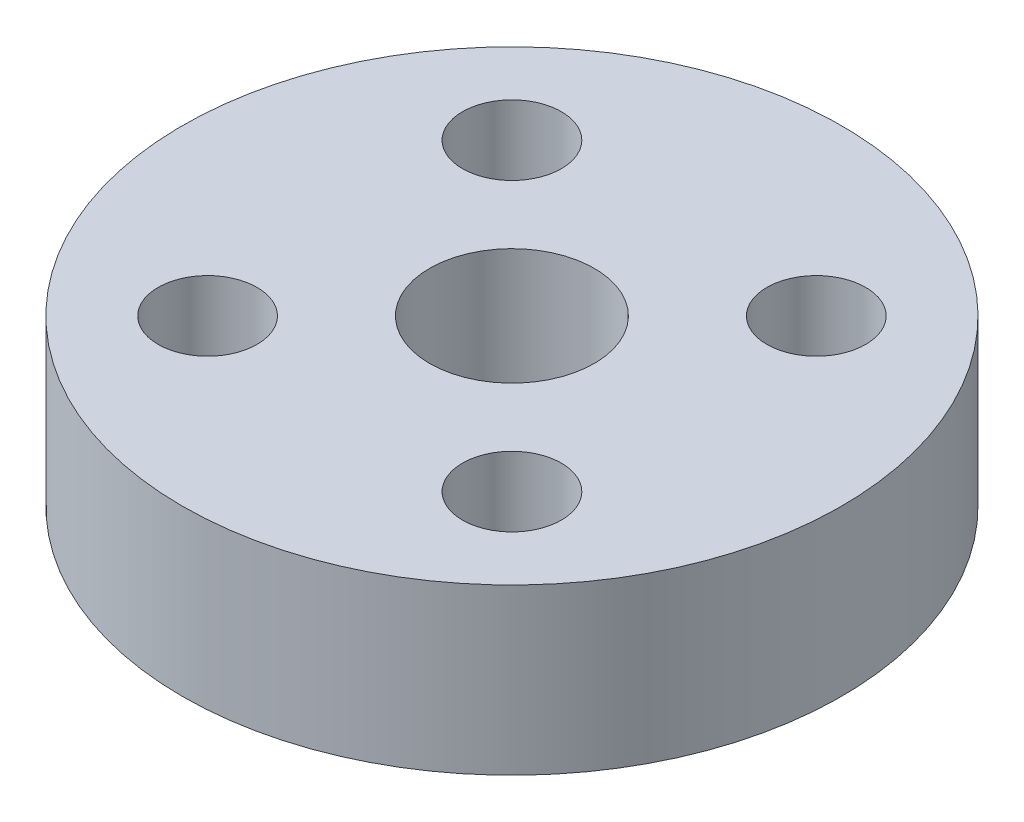
SolidWorks part; units mm, degrees
ref_plane "Спереди" through (0, 0, 0) normal (0, 0, 1) x (1, 0, 0)
ref_plane "Сверху" through (0, 0, 0) normal (0, 1, 0) x (1, 0, 0)
ref_plane "Справа" through (0, 0, 0) normal (1, 0, 0) x (0, 0, -1)
sketch "Эскиз1" plane through (0, 0, 0) normal (0, 1, 0) x (1, 0, 0)
  line L0 (0, 0) -> (0, 10)
  line L1 (0, 0) -> (7.0711, 7.0711)
  circle A0 centre (0, 0) radius 10
  circle A1 centre (0, 0) radius 2.5
  circle A2 centre (4.6174, 4.6174) radius 1.5
  circle A3 centre (4.6174, -4.6174) radius 1.5
  circle A4 centre (-4.6174, -4.6174) radius 1.5
  circle A5 centre (-4.6174, 4.6174) radius 1.5
  point P17 (0, 0)
  dimension "D1" = 20
  dimension "D3" = 5
  dimension "D5" = 3
  dimension "D2" = 45
  dimension "D4" = 6.53
  dimension "D6" = 4
extrude "Бобышка-Вытянуть1" add sketch "Эскиз1" along normal blind 5 contours A2 L1 A0 L0 A1 | A2 L1 A1 L0 A0 A5 A4 A3
ref_plane "Плоскость1" through (10, 0, 0) normal (1, 0, 0) x (0, 0, -1)
sketch "Sketch1" plane through (0, 0, 0) normal (0, 1, 0) x (1, 0, 0)
  circle A0 centre (0, 0) radius 158.75
  dimension "D1" = 317.5
